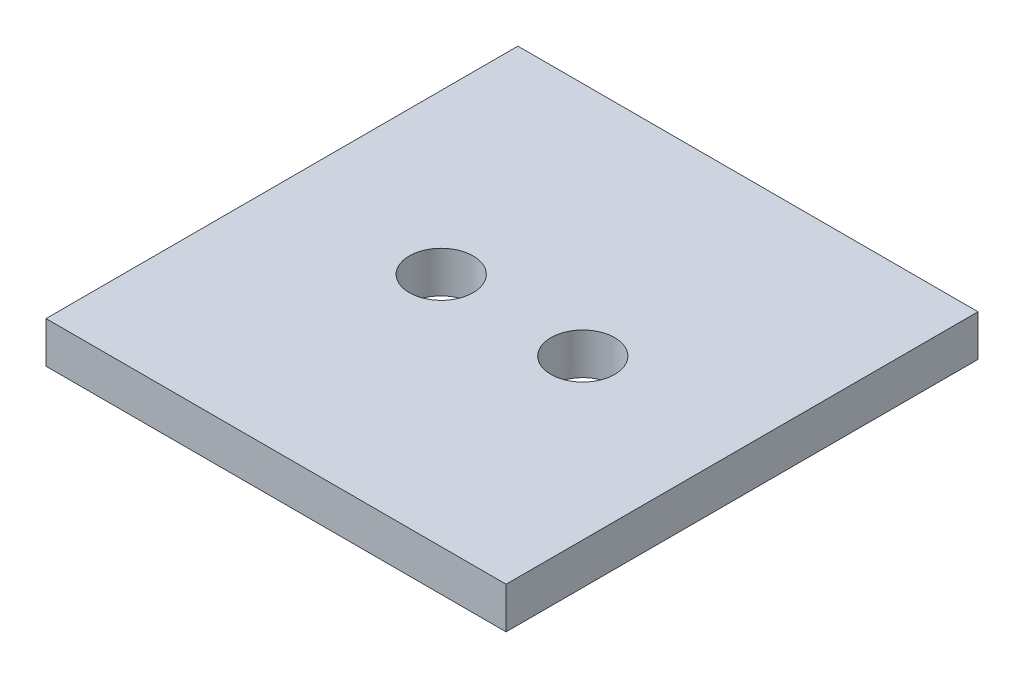
SolidWorks part; units mm, degrees
ref_plane "Front Plane" through (0, 0, 0) normal (0, 0, 1) x (1, 0, 0)
ref_plane "Top Plane" through (0, 0, 0) normal (0, 1, 0) x (1, 0, 0)
ref_plane "Right Plane" through (0, 0, 0) normal (1, 0, 0) x (0, 0, -1)
sketch "Sketch1" plane through (0, 0, 0) normal (0, 1, 0) x (1, 0, 0)
  line L1 (-9.75, -10) -> (9.75, -10)
  line L2 (-9.75, -10) -> (-9.75, 10)
  line L3 (-9.75, 10) -> (9.75, 10)
  line L4 (9.75, -10) -> (9.75, 10)
  line L5 (-9.75, -10) -> (9.75, 10) construction
  line L6 (-9.75, 10) -> (9.75, -10) construction
  point P0 (0, 0)
  dimension "D1" = 20
  dimension "D2" = 19.5
extrude "Boss-Extrude1" add sketch "Sketch1" along normal blind 1.75
sketch "Sketch3" plane through (0, 1.75, 0) normal (0, 1, 0) x (1, 0, 0)
  line L0 (0, 0) -> (-12.8331, 0) construction
  line L1 (0, -0.9625) -> (0, 0.9625) construction
  circle A0 centre (0, 0) radius 6 construction
  point P1 (-3, 0)
  point P7 (3, 0)
  dimension "D2" = 12
  dimension "D1" = 3
hole_wizard "Tap Drill for #6-32 Tap1" positions "Sketch3" profile "Sketch4" hole size "#6-32" standard "ANSI Inch"
sketch "Sketch4" plane through (3, 1.75, 0) normal (1, 0, 0) x (0, 0, 1)
  line L0 (0, 0) -> (0, 10.8127)
  line L1 (0, 10.8127) -> (1.3525, 10)
  line L2 (1.3525, 10) -> (1.3525, 0)
  line L5 (1.3525, 0) -> (0, 0)
  line L10 (0, 10.8127) -> (-1.3525, 10) construction
  line L11 (0, -6.35) -> (0, 107.95) construction
  dimension "Hole Dia." = 2.7051
  dimension "Hole Depth" = 10
  dimension "Drill Angle" = 118
